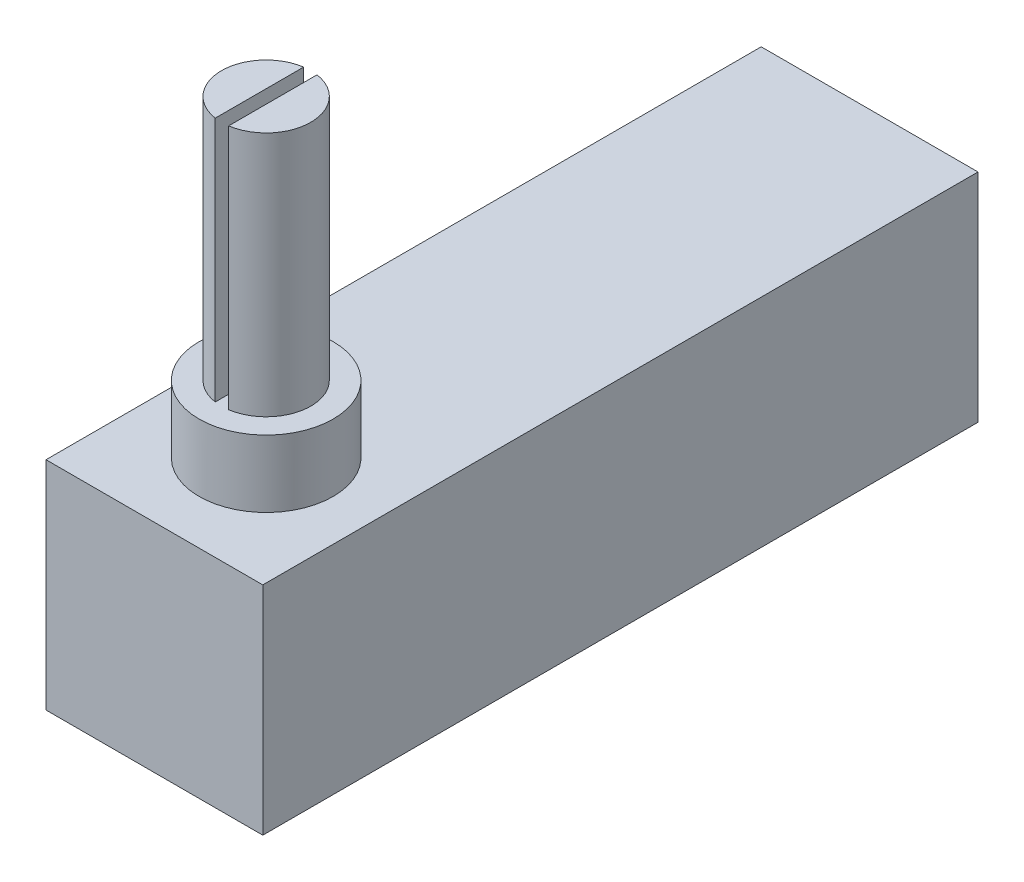
SolidWorks part; units mm, degrees
ref_plane "Front Plane" through (0, 0, 0) normal (0, 0, 1) x (1, 0, 0)
ref_plane "Top Plane" through (0, 0, 0) normal (0, 1, 0) x (1, 0, 0)
ref_plane "Right Plane" through (0, 0, 0) normal (1, 0, 0) x (0, 0, -1)
sketch "Sketch1" plane through (0, 0, 0) normal (0, 0, 1) x (1, 0, 0)
  line L1 (-6.1595, 0) -> (6.1595, 0)
  line L2 (-6.1595, 0) -> (-6.1595, -12.319)
  line L3 (-6.1595, -12.319) -> (6.1595, -12.319)
  line L4 (6.1595, 0) -> (6.1595, -12.319)
  point P4 (0, 0)
  dimension "D1" = 12.319
  dimension "D2" = 12.319
extrude "Boss-Extrude1" add sketch "Sketch1" along normal blind 40.64
sketch "Sketch2" plane through (0, 0, 0) normal (0, 1, 0) x (1, 0, 0)
  line L1 (6.1595, -40.64) -> (-6.1595, -40.64) construction
  line L2 (0, -30.1313) -> (0, -38.7674) construction
  line L4 (-0.381, -31.7787) -> (-0.381, -36.8013)
  line L5 (0.381, -31.7787) -> (0.381, -36.8013)
  arc A3 (-0.381, -31.7787) -> (-0.381, -36.8013) centre (0, -34.29) ccw
  arc A4 (0.381, -36.8013) -> (0.381, -31.7787) centre (0, -34.29) ccw
  dimension "D1" = 5.08
  dimension "D2" = 6.35
  dimension "D3" = 0.762
extrude "Boss-Extrude2" add sketch "Sketch2" along normal blind 17.78
sketch "Sketch3" plane through (0, 0, 0) normal (0, 1, 0) x (1, 0, 0)
  circle A1 centre (0, -34.29) radius 3.81
  arc A3 (-0.381, -31.7787) -> (-0.381, -36.8013) centre (0, -34.29) ccw construction
  point P1 (0, 0)
  dimension "D1" = 1.27
extrude "Boss-Extrude3" add sketch "Sketch3" along normal blind 3.81
